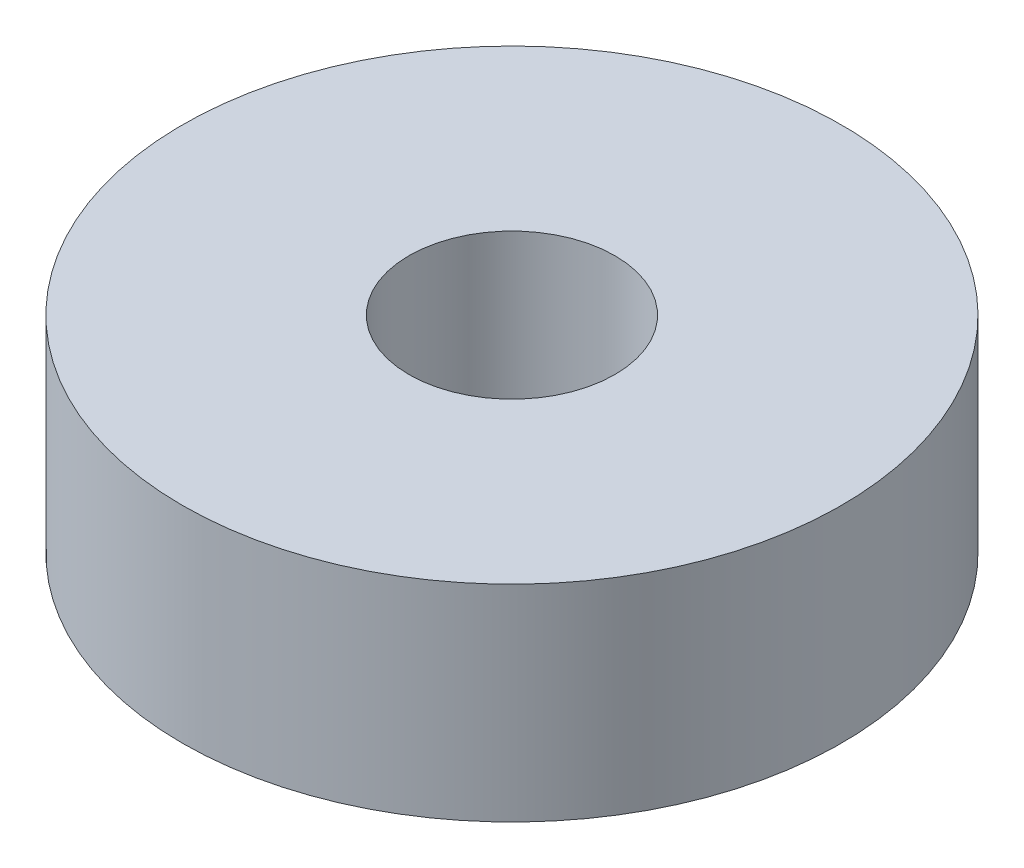
SolidWorks part; units mm, degrees
ref_plane "Front Plane" through (0, 0, 0) normal (0, 0, 1) x (1, 0, 0)
ref_plane "Top Plane" through (0, 0, 0) normal (0, 1, 0) x (1, 0, 0)
ref_plane "Right Plane" through (0, 0, 0) normal (1, 0, 0) x (0, 0, -1)
sketch "Sketch1" plane through (0, 0, 0) normal (0, 1, 0) x (1, 0, 0)
  circle A0 centre (0, 0) radius 2.5
  circle A1 centre (0, 0) radius 8
  dimension "D1" = 5
  dimension "D2" = 16
extrude "Boss-Extrude1" add sketch "Sketch1" along normal blind 5
